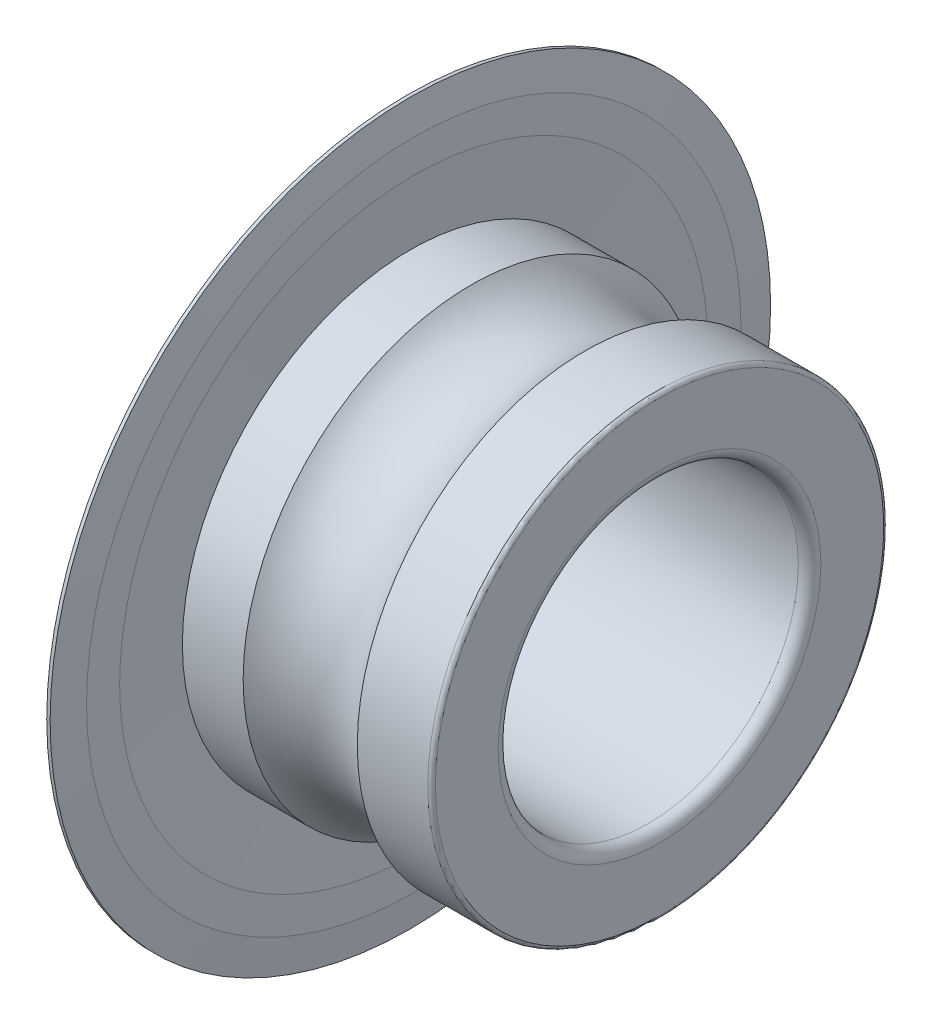
SolidWorks part; units mm, degrees
ref_plane "Ebene vorne" through (0, 0, 0) normal (0, 0, 1) x (1, 0, 0)
ref_plane "Ebene oben" through (0, 0, 0) normal (0, 1, 0) x (1, 0, 0)
ref_plane "Ebene rechts" through (0, 0, 0) normal (1, 0, 0) x (0, 0, -1)
ref_plane "Ebene1" through (0, 0, 0) normal (0, 0, 1) x (1, 0, 0)
sketch "Skizze1" plane through (0, 0, 0) normal (0, 0, 1) x (1, 0, 0)
  line L0 (0, 5.975) -> (0, 4.3)
  line L1 (0.3, 4) -> (6.7, 4)
  line L2 (7, 4.3) -> (7, 5.975)
  line L3 (6.9, 6.075) -> (5.0207, 6.075)
  line L4 (1.9793, 6.075) -> (0.1, 6.075)
  line L5 (50, 0) -> (-50, 0) construction
  arc A0 (0, 4.3) -> (0.3, 4) centre (0.3, 4.3) ccw
  arc A1 (6.7, 4) -> (7, 4.3) centre (6.7, 4.3) ccw
  arc A2 (7, 5.975) -> (6.9, 6.075) centre (6.9, 5.975) ccw
  arc A3 (5.0207, 6.075) -> (1.9793, 6.075) centre (3.5, 7.35) cw
  arc A4 (0.1, 6.075) -> (0, 5.975) centre (0.1, 5.975) ccw
revolve "Rotation1" add sketch "Skizze1" angle 360 about L5
ref_plane "Ebene2" through (0, 0, 0) normal (0, 0, 1) x (1, 0, 0)
sketch "Skizze2" plane through (0, 0, 0) normal (0, 0, 1) x (1, 0, 0)
  line L0 (0.27, 9.6) -> (0.315, 8.7188)
  line L1 (0.315, 8.7188) -> (0.27, 7.8375)
  line L2 (0.27, 7.8375) -> (0.27, 6.075)
  line L3 (0.27, 6.075) -> (0.36, 6.075)
  line L4 (0.36, 6.075) -> (0.45, 7.8375)
  line L5 (0.45, 7.8375) -> (0.45, 8.7188)
  line L6 (0.45, 8.7188) -> (0.36, 9.6)
  line L7 (0.36, 9.6) -> (0.27, 9.6)
  line L8 (50, 0) -> (-50, 0) construction
revolve "Rotation2" add sketch "Skizze2" angle 360 about L8
